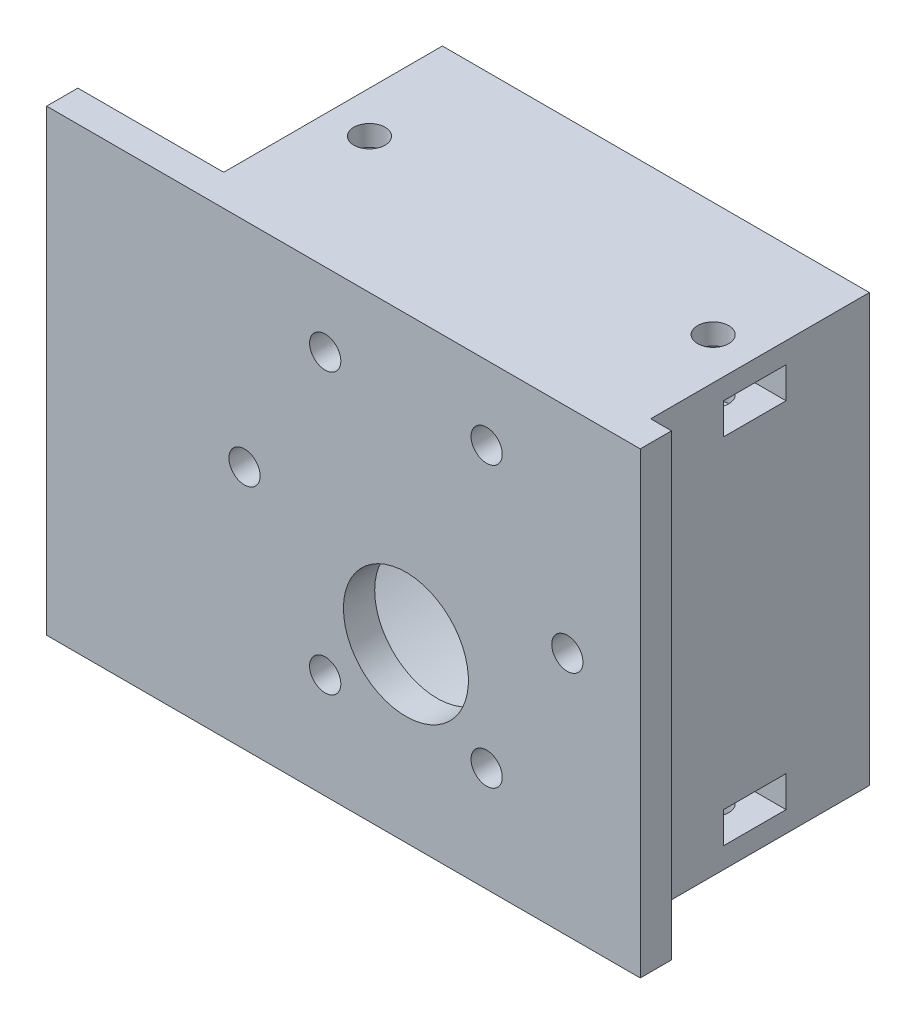
SolidWorks part; units mm, degrees
ref_plane "前视基准面" through (0, 0, 0) normal (0, 0, 1) x (1, 0, 0)
ref_plane "上视基准面" through (0, 0, 0) normal (0, 1, 0) x (1, 0, 0)
ref_plane "右视基准面" through (0, 0, 0) normal (1, 0, 0) x (0, 0, -1)
sketch "草图1" plane through (0, 0, 0) normal (0, 0, 1) x (1, 0, 0)
  line L1 (-34.5, 20.5) -> (34.5, 20.5)
  line L2 (-34.5, 20.5) -> (-34.5, -23.5)
  line L3 (-34.5, -23.5) -> (34.5, -23.5)
  line L4 (34.5, 20.5) -> (34.5, -23.5)
  point P4 (0, -23.5)
  dimension "D1" = 20.5
  dimension "D2" = 23.5
  dimension "D3" = 0
  dimension "D4" = 34.5
extrude "固定板" add sketch "草图1" along normal blind 3
sketch "草图2" plane through (0, 0, 0) normal (0, 0, -1) x (-1, 0, 0)
  circle A0 centre (-15.5, 0) radius 1.5
  circle A1 centre (-7.75, 13.4234) radius 1.5
  circle A2 centre (7.75, 13.4234) radius 1.5
  circle A3 centre (15.5, 0) radius 1.5
  circle A4 centre (7.75, -13.4234) radius 1.5
  circle A5 centre (-7.75, -13.4234) radius 1.5
  circle A6 centre (0, -7) radius 6
  point P15 (0, 0)
  dimension "D1" = 3
  dimension "D5" = 12
  dimension "D2" = 15.5
  dimension "D4" = 7
  dimension "D3" = 6
extrude "电机螺丝孔" cut sketch "草图2" against normal blind 3
sketch "草图4" plane through (0, 0, 0) normal (0, 0, -1) x (-1, 0, 0)
  circle A0 centre (0, 0) radius 18.5
  circle A1 centre (0, 0) radius 20.5
  dimension "D1" = 37
  dimension "D2" = 2
extrude "减速器箍（内）" add sketch "草图4" along normal blind 21
sketch "草图13" plane through (0, 0, 0) normal (0, 0, -1) x (-1, 0, 0)
  line L1 (20.5, -18.5) -> (-20.5, -18.5)
  line L2 (20.5, -18.5) -> (20.5, 18.5)
  line L3 (20.5, 18.5) -> (-20.5, 18.5)
  line L4 (-20.5, -18.5) -> (-20.5, 18.5)
  line L5 (20.5, -18.5) -> (-20.5, 18.5) construction
  line L6 (20.5, 18.5) -> (-20.5, -18.5) construction
  point P0 (0, 0)
  circle M4 centre (0, 0) radius 20.5
  dimension "D1" = 37
  dimension "D2" = 41
extrude "减速器箍（外）" add sketch "草图13" along normal blind 21 contours L4 L3 M4 | L4 L1 M4 | L1 L2 M4 | L2 L3 M4
sketch "草图20" plane through (0, -18.5, 0) normal (0, -1, 0) x (1, 0, 0)
  line L0 (20.5, -21) -> (20.5, 0) construction
  line L2 (19.1547, -7) -> (14.7679, -7)
  line L3 (14.7679, -7) -> (13.0359, -10)
  line L4 (13.0359, -10) -> (14.7679, -13)
  line L5 (14.7679, -13) -> (19.1547, -13)
  line L7 (-34.5, 0) -> (34.5, 0) construction
  line L8 (0, -5.0303) -> (0, -13.9025)
  line L9 (19.1547, -7) -> (20.5, -7)
  line L10 (19.1547, -7) -> (19.1547, -13)
  line L11 (19.1547, -13) -> (20.5, -13)
  line L12 (20.5, -7) -> (20.5, -13)
  line L13 (-20.5, -7) -> (-20.5, -13)
  line L14 (-19.1547, -13) -> (-20.5, -13)
  line L15 (-19.1547, -7) -> (-19.1547, -13)
  line L16 (-19.1547, -7) -> (-20.5, -7)
  line L18 (-14.7679, -13) -> (-19.1547, -13)
  line L19 (-13.0359, -10) -> (-14.7679, -13)
  line L20 (-14.7679, -7) -> (-13.0359, -10)
  line L21 (-19.1547, -7) -> (-14.7679, -7)
  line L23 (19.0981, -8.5) -> (17.6547, -6) [skipped]
  line L24 (19.0981, -11.5) -> (20.5415, -9) [skipped]
  circle A0 centre (16.5, -10) radius 2.5 construction
  circle A1 centre (-16.5, -10) radius 2.5 construction
  line M7 (20.5, -21) -> (20.5, 0)
  dimension "D1" = 6
  dimension "D2" = 4
  dimension "D3" = 10
extrude "螺母口（下）" cut sketch "草图20" against normal blind 3 contours L21 L15 L18 L19 L20 | L15 L16 L13 L14 | L10 L2 L3 L4 L5 | L10 L11 L9 M7
sketch "草图21" plane through (0, 18.5, 0) normal (0, 1, 0) x (1, 0, 0)
  line L0 (8.8318, 0) -> (20.5, 0) construction
  line L1 (0, 5.8025) -> (0, 15.5143)
  line L2 (19.1547, 13) -> (14.7679, 13)
  line L3 (14.7679, 13) -> (13.0359, 10)
  line L4 (13.0359, 10) -> (14.7679, 7)
  line L5 (14.7679, 7) -> (19.1547, 7)
  line L6 (-20.5, 13) -> (-20.5, 7)
  line L7 (20.5, 21) -> (20.5, 0) construction
  line L8 (-19.1547, 7) -> (-20.5, 7)
  line L9 (19.1547, 13) -> (20.5, 13)
  line L10 (19.1547, 13) -> (19.1547, 7)
  line L11 (19.1547, 7) -> (20.5, 7)
  line L12 (20.5, 13) -> (20.5, 7)
  line L13 (19.0981, 11.5) -> (17.6547, 14) [skipped]
  line L14 (19.0981, 8.5) -> (20.5415, 11) [skipped]
  line L15 (-19.1547, 13) -> (-19.1547, 7)
  line L16 (-19.1547, 13) -> (-20.5, 13)
  line L17 (-14.7679, 7) -> (-19.1547, 7)
  line L18 (-13.0359, 10) -> (-14.7679, 7)
  line L19 (-14.7679, 13) -> (-13.0359, 10)
  line L20 (-19.1547, 13) -> (-14.7679, 13)
  circle A0 centre (16.5, 10) radius 2.5 construction
  circle A1 centre (-16.5, 10) radius 2.5 construction
  line M5 (20.5, 0) -> (20.5, 21)
  dimension "D1" = 6
  dimension "D2" = 10
  dimension "D3" = 4
extrude "螺母口（上）" cut sketch "草图21" against normal blind 3 contours L10 L2 L3 L4 L5 | L10 L11 L9 M5 | L20 L15 L17 L18 L19 | L15 L16 L6 L8
sketch "草图11" plane through (0, 0, 0) normal (0, 0, -1) x (-1, 0, 0)
  line L1 (-20.5, 20.5) -> (20.5, 20.5)
  line L2 (-20.5, 20.5) -> (-20.5, 18.5)
  line L3 (-20.5, 18.5) -> (20.5, 18.5)
  line L4 (20.5, 20.5) -> (20.5, 18.5)
  line L5 (-20.5, -20.5) -> (20.5, -20.5)
  line L6 (-20.5, -20.5) -> (-20.5, -18.5)
  line L7 (-20.5, -18.5) -> (20.5, -18.5)
  line L8 (20.5, -20.5) -> (20.5, -18.5)
  point P0 (0, -18.5)
  point P10 (0, 18.5)
  dimension "D1" = 2
  dimension "D2" = 2
  dimension "D3" = 41
  dimension "D4" = 41
  dimension "D5" = 18.5
  dimension "D6" = 18.5
  dimension "D7" = 0
  dimension "D8" = 0
extrude "平连接面" add sketch "草图11" along normal blind 21
sketch "草图16" plane through (0, -20.5, 0) normal (0, -1, 0) x (1, 0, 0)
  line L0 (-34.5, 0) -> (34.5, 0) construction
  line L1 (-20.5, -21) -> (-20.5, 0) construction
  line L2 (0, -5.1003) -> (0, -11.841)
  circle A0 centre (-16.5, -10) radius 1.5
  circle A1 centre (16.5, -10) radius 1.5
  dimension "D1" = 3
  dimension "D2" = 10
  dimension "D3" = 4
extrude "螺丝孔（下）" cut sketch "草图16" against normal blind 6.5 contours A0 | A1
sketch "草图17" plane through (0, 20.5, 0) normal (0, 1, 0) x (1, 0, 0)
  line L0 (-20.5, 21) -> (-20.5, 0) construction
  line L2 (-20.5, 0) -> (-34.5, 0) construction
  line L3 (0, 4.9171) -> (0, 12.0487)
  circle A0 centre (-16.5, 10) radius 1.5
  circle A1 centre (16.5, 10) radius 1.5
  dimension "D1" = 3
  dimension "D2" = 4
  dimension "D3" = 10
extrude "螺丝孔（上）" cut sketch "草图17" against normal blind 6.5 contours A0 | A1
sketch "草图22" plane through (0, 0, 0) normal (0, 0, -1) x (-1, 0, 0)
  line L0 (34.5, -23.5) -> (-34.5, -23.5) construction
  line L1 (-34.5, 20.5) -> (-22.5, 20.5)
  line L2 (-34.5, 20.5) -> (-34.5, -23.5)
  line L3 (-34.5, -23.5) -> (-22.5, -23.5)
  line L4 (-22.5, 20.5) -> (-22.5, -23.5)
  line L5 (-20.5, -20.5) -> (-20.5, 20.5) construction
  dimension "D1" = 2
extrude "去除多余挡板" cut sketch "草图22" against normal blind 3
fillet "圆角1" radius 1 1 edges at (-18.5, 0, 0)
